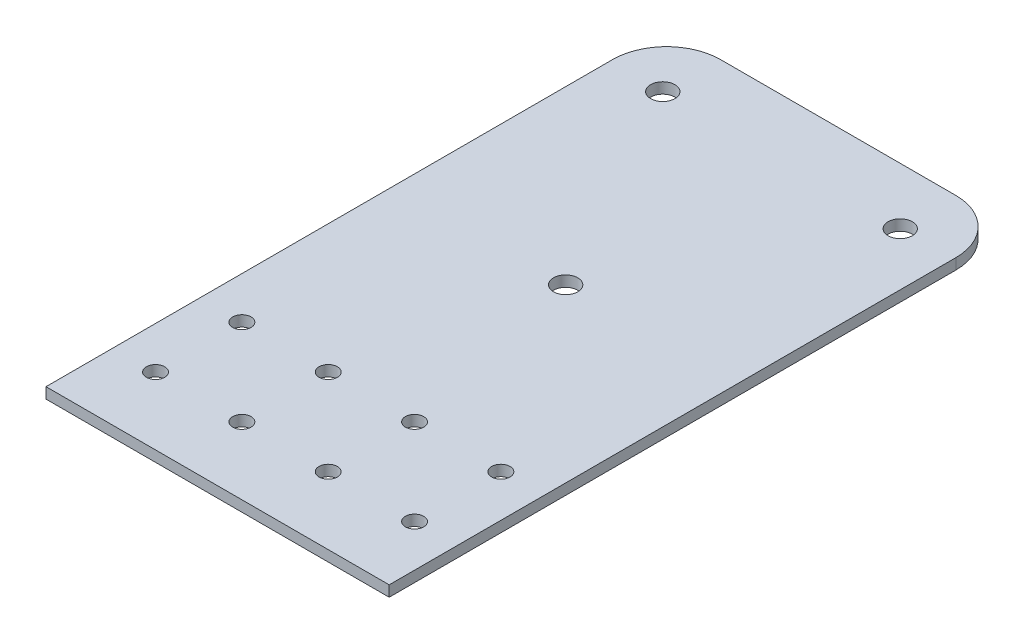
SolidWorks part; units mm, degrees
material "6061 Alloy"
ref_plane "Front Plane" through (0, 0, 0) normal (0, 0, 1) x (1, 0, 0)
ref_plane "Top Plane" through (0, 0, 0) normal (0, 1, 0) x (1, 0, 0)
ref_plane "Right Plane" through (0, 0, 0) normal (1, 0, 0) x (0, 0, -1)
sketch "Sketch2" plane through (0, 0, 0) normal (1, 0, 0) x (0, 0, -1)
  line L0 (0, 0) -> (0, 2)
  line L1 (0, 2) -> (-35, 2)
  line L2 (-35, 2) -> (-55, 2)
  line L3 (-55, 2) -> (-115, 2)
  line L4 (0, 0) -> (-35, 0)
  line L5 (-115, 2) -> (-115, 0)
  line L6 (-35, 0) -> (-55, 0)
  line L7 (-55, 0) -> (-115, 0)
  line L8 (-2, 0) -> (-2, 0) construction
  line L9 (-2, 0) -> (-35, 0) construction
  dimension "D2" = 60
  dimension "D3" = 115
  dimension "D5" = 35
  dimension "D1" = 2
extrude "Sheet Extrude" add sketch "Sketch2" along normal mid plane 63.6
hole_wizard "M3 Clearance Hole1" positions "Sketch5" profile "Sketch6" hole size "M3" standard "ANSI Metric"
sketch "Sketch5" plane through (0, 2, 0) normal (0, 1, 0) x (1, 0, 0)
  line L0 (0, -127.4881) -> (0, -27.1774) construction
  line L2 (31.8, -115) -> (-31.8, -115) construction
  point P0 (-24, -102.5)
  point P2 (-24, -86.5)
  point P4 (-8, -86.5)
  point P6 (-8, -102.5)
  point P16 (24, -102.5)
  point P17 (8, -102.5)
  point P18 (8, -86.5)
  point P19 (24, -86.5)
  dimension "D1" = 16
  dimension "D2" = 16
  dimension "D3" = 8
  dimension "D4" = 12.5
sketch "Sketch6" plane through (-24, 2, 102.5) normal (1, 0, 0) x (0, 0, 1)
  line L0 (0, 0) -> (0, 9.5215)
  line L1 (0, 9.5215) -> (1.7, 8.5)
  line L2 (1.7, 8.5) -> (1.7, 0)
  line L5 (1.7, 0) -> (0, 0)
  line L10 (0, 9.5215) -> (-1.7, 8.5) construction
  line L11 (0, -6.35) -> (0, 107.95) construction
  dimension "Hole Dia." = 3.4
  dimension "Hole Depth" = 8.5
  dimension "Drill Angle" = 118
hole_wizard "M4 Clearance Hole1" positions "Sketch9" profile "Sketch10" hole size "M4" standard "ANSI Metric"
sketch "Sketch9" plane through (0, 2, 0) normal (0, 1, 0) x (1, 0, 0)
  circle A0 centre (8, -86.5) radius 1.7 construction
  point P0 (0, -50.5)
  point P5 (22, -10.5)
  point P7 (-22, -10.5)
  dimension "D1" = 36
  dimension "D2" = 22
  dimension "D3" = 44
  dimension "D4" = 40
sketch "Sketch10" plane through (0, 2, 50.5) normal (1, 0, 0) x (0, 0, 1)
  line L0 (0, 0) -> (0, 8.8519)
  line L1 (0, 8.8519) -> (2.25, 7.5)
  line L2 (2.25, 7.5) -> (2.25, 0)
  line L5 (2.25, 0) -> (0, 0)
  line L10 (0, 8.8519) -> (-2.25, 7.5) construction
  line L11 (0, -6.35) -> (0, 107.95) construction
  dimension "Hole Dia." = 4.5
  dimension "Hole Depth" = 7.5
  dimension "Drill Angle" = 118
fillet "Fillet1" radius 10 2 edges at (31.8, 1, 0) (-31.8, 1, 0)
